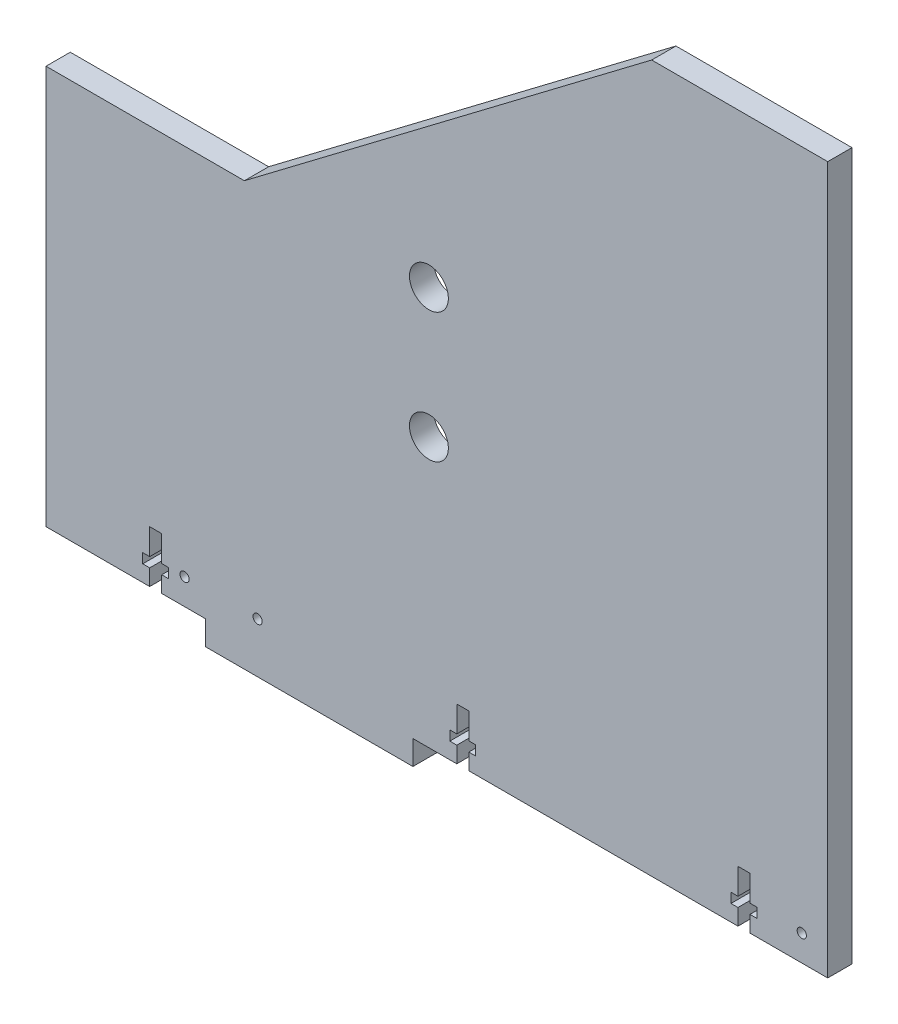
SolidWorks part; units mm, degrees
ref_plane "Front Plane" through (0, 0, 0) normal (0, 0, 1) x (1, 0, 0)
ref_plane "Top Plane" through (0, 0, 0) normal (0, 1, 0) x (1, 0, 0)
ref_plane "Right Plane" through (0, 0, 0) normal (1, 0, 0) x (0, 0, -1)
sketch "Sketch1" plane through (0, 0, 0) normal (0, 0, 1) x (1, 0, 0)
  line L0 (0, 0) -> (0, 97.7138)
  line L1 (0, 97.7138) -> (35.9029, 97.7138)
  line L2 (35.9029, 97.7138) -> (135.6995, 173.228)
  line L3 (135.6995, 173.228) -> (178.8287, 173.228)
  line L4 (178.8287, 173.228) -> (178.8287, 0)
  line L5 (178.8287, 0) -> (0, 0)
  dimension "D1" = 97.7138
  dimension "D2" = 173.228
  dimension "D3" = 35.9029
  dimension "D5" = 43.1292
  dimension "D6" = 142.9258
extrude "Boss-Extrude1" add sketch "Sketch1" along normal blind 5.9436
sketch "Sketch3" plane through (0, 0, 5.9436) normal (0, 0, 1) x (1, 0, 0)
  line L0 (178.8287, 0) -> (178.8287, 173.228) construction
  line L1 (0, 0) -> (178.8287, 0) construction
  circle A0 centre (81.1149, 97.7138) radius 4.7625
  dimension "D1" = 9.525
  dimension "D2" = 97.7138
  dimension "D3" = 97.7138
extrude "Cut-Extrude1" cut sketch "Sketch3" against normal through all
sketch "Sketch4" plane through (0, 0, 5.9436) normal (0, 0, 1) x (1, 0, 0)
  line L0 (12.7, 0) -> (12.7, 3.9688)
  line L1 (0, 0) -> (178.8287, 0) construction
  line L2 (12.7, 3.9688) -> (10.9982, 3.9688)
  line L3 (10.9982, 3.9688) -> (10.9982, 6.35)
  line L4 (10.9982, 6.35) -> (12.7, 6.35)
  line L5 (12.7, 6.35) -> (12.7, 12.7)
  line L6 (12.7, 12.7) -> (15.6464, 12.7)
  line L7 (15.6464, 12.7) -> (15.6464, 6.35)
  line L8 (15.6464, 6.35) -> (17.3482, 6.35)
  line L9 (17.3482, 6.35) -> (17.3482, 3.9688)
  line L10 (17.3482, 3.9688) -> (15.6464, 3.9688)
  line L11 (15.6464, 3.9688) -> (15.6464, 0)
  line L12 (156.8323, 0) -> (156.8323, 3.9688)
  line L13 (156.8323, 3.9688) -> (155.1305, 3.9688)
  line L14 (155.1305, 3.9688) -> (155.1305, 6.35)
  line L15 (155.1305, 6.35) -> (156.8323, 6.35)
  line L16 (156.8323, 6.35) -> (156.8323, 12.7)
  line L17 (156.8323, 12.7) -> (159.7787, 12.7)
  line L18 (159.7787, 12.7) -> (159.7787, 6.35)
  line L19 (159.7787, 6.35) -> (161.4805, 6.35)
  line L20 (161.4805, 6.35) -> (161.4805, 3.9688)
  line L21 (161.4805, 3.9688) -> (159.7787, 3.9688)
  line L22 (159.7787, 3.9688) -> (159.7787, 0)
  line L23 (178.8287, 0) -> (178.8287, 173.228) construction
  line L24 (87.9412, 0) -> (87.9412, 3.9688)
  line L25 (87.9412, 3.9688) -> (86.2394, 3.9688)
  line L26 (86.2394, 3.9688) -> (86.2394, 6.35)
  line L27 (86.2394, 6.35) -> (87.9412, 6.35)
  line L28 (87.9412, 6.35) -> (87.9412, 12.7)
  line L29 (87.9412, 12.7) -> (90.8876, 12.7)
  line L30 (90.8876, 12.7) -> (90.8876, 6.35)
  line L31 (90.8876, 6.35) -> (92.5894, 6.35)
  line L32 (92.5894, 6.35) -> (92.5894, 3.9688)
  line L33 (92.5894, 3.9688) -> (90.8876, 3.9688)
  line L34 (90.8876, 3.9688) -> (90.8876, 0)
  line L35 (87.9412, 0) -> (90.8876, 0)
  point P27 (89.4144, 0)
  point P42 (89.4144, 0)
  line M11 (0, 0) -> (178.8287, 0)
  dimension "D1" = 2.9464
  dimension "D2" = 6.35
  dimension "D3" = 12.7
  dimension "D4" = 2.3813
  dimension "D5" = 6.35
  dimension "D6" = 6.35
  dimension "D7" = 12.7
  dimension "D8" = 2.9464
  dimension "D9" = 6.35
  dimension "D10" = 2.3813
  dimension "D11" = 6.35
  dimension "D12" = 6.35
  dimension "D13" = 19.05
  dimension "D14" = 12.7
  dimension "D15" = 2.9464
  dimension "D16" = 6.35
  dimension "D17" = 2.3813
  dimension "D18" = 6.35
  dimension "D19" = 6.35
  dimension "D20" = 12.7
extrude "Cut-Extrude2" cut sketch "Sketch4" against normal through all contours L11 L10 L9 L8 L7 L6 L5 L4 L3 L2 L0 M11 | L34 L33 L32 L31 L30 L29 L28 L27 L26 L25 L24 M11 | L22 L21 L20 L19 L18 L17 L16 L15 L14 L13 L12 M11
sketch "Sketch5" plane through (0, 0, 5.9436) normal (0, 0, 1) x (1, 0, 0)
  line L0 (26.3938, 0) -> (26.3938, -5.9436)
  line L1 (15.6464, 0) -> (87.9412, 0) construction
  line L2 (26.3938, -5.9436) -> (77.1938, -5.9436)
  line L3 (77.1938, -5.9436) -> (77.1938, 0)
  line L4 (77.1938, 0) -> (26.3938, 0)
  line L5 (15.6464, 0) -> (26.3938, 0) construction
  line L6 (77.1938, 0) -> (87.9412, 0) construction
  dimension "D1" = 50.8
  dimension "D2" = 5.9436
extrude "Boss-Extrude2" add sketch "Sketch5" against normal up to surface (5.9436 mm away) up to face at (85.8774, 97.7138, 0)
sketch "Sketch6" plane through (0, 0, 5.9436) normal (0, 0, 1) x (1, 0, 0)
  circle A1 centre (81.1149, 65.9638) radius 4.7625
  dimension "D1" = 9.525
extrude "Cut-Extrude3" cut sketch "Sketch6" against normal through all
sketch "Sketch7" plane through (0, 0, 5.9436) normal (0, 0, 1) x (1, 0, 0)
  line L1 (0, 0) -> (-12.7, 0)
  line L2 (0, 0) -> (0, 97.7138)
  line L3 (0, 97.7138) -> (-12.7, 97.7138)
  line L4 (-12.7, 0) -> (-12.7, 97.7138)
  line L5 (0, 0) -> (-12.7, 97.7138) construction
  line L6 (0, 97.7138) -> (-12.7, 0) construction
  point P4 (-6.35, 48.8569)
  dimension "D1" = 12.7
extrude "Boss-Extrude3" add sketch "Sketch7" against normal up to surface (5.9436 mm away) up to face at (85.8774, 65.9638, 0)
sketch "Sketch8" plane through (0, 0, 5.9436) normal (0, 0, 1) x (1, 0, 0)
  line L0 (-12.7, 0) -> (12.7, 0) construction
  line L2 (178.8287, 0) -> (178.8287, 173.228) construction
  line L3 (-12.7, 97.7138) -> (-12.7, 0) construction
  circle A0 centre (39.1414, 6.35) radius 1.1303
  circle A1 centre (172.4787, 6.35) radius 1.1303
  circle A2 centre (21.2344, 6.35) radius 1.1303
  dimension "D1" = 2.2606
  dimension "D3" = 51.8414
  dimension "D2" = 6.35
  dimension "D4" = 6.35
  dimension "D5" = 17.907
extrude "Cut-Extrude4" cut sketch "Sketch8" against normal through all
